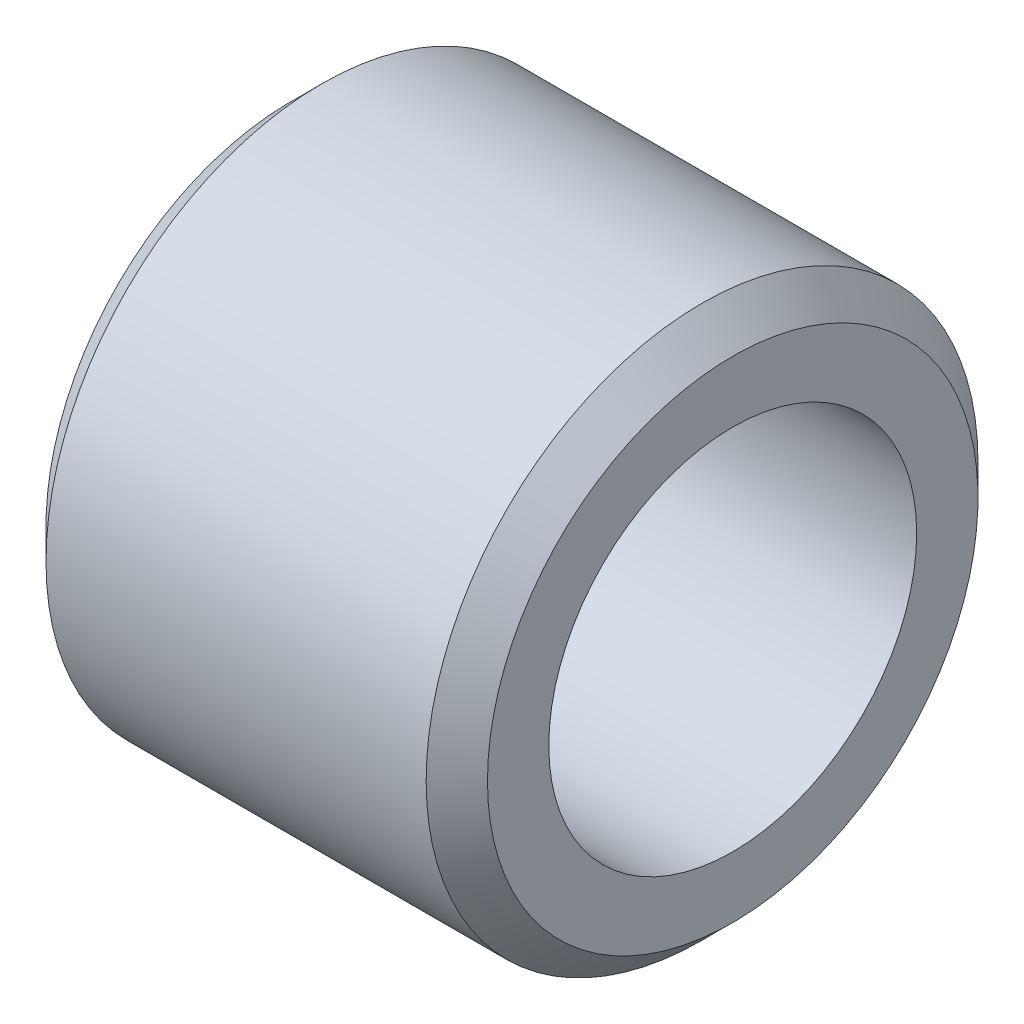
SolidWorks part; units mm, degrees
material "A5052S"
ref_plane "Front Plane" through (0, 0, 0) normal (0, 0, 1) x (1, 0, 0)
ref_plane "Top Plane" through (0, 0, 0) normal (0, 1, 0) x (1, 0, 0)
ref_plane "Right Plane" through (0, 0, 0) normal (1, 0, 0) x (0, 0, -1)
sketch "Sketch1" plane through (0, 0, 0) normal (0, 0, 1) x (1, 0, 0)
  line L0 (0, 0) -> (7.2, 0) construction
  line L1 (7.2, 3) -> (0, 3)
  line L2 (0, 3) -> (0, 4.5)
  line L4 (0, 4.5) -> (7.2, 4.5)
  line L6 (7.2, 4.5) -> (7.2, 3)
  dimension "D_s" = 6
  dimension "D" = 9
  dimension "L" = 7.2
revolve "Revolve1" add sketch "Sketch1" angle 360 about L0
chamfer "Chamfer1" distance 0.5 angle 45 2 edges at (0, 0, 4.5) (7.2, 0, 4.5)
equation "\"D1@Chamfer1\" = if ( \"L@Sketch1\" < 3 , 0.2 , 0.5 )"
